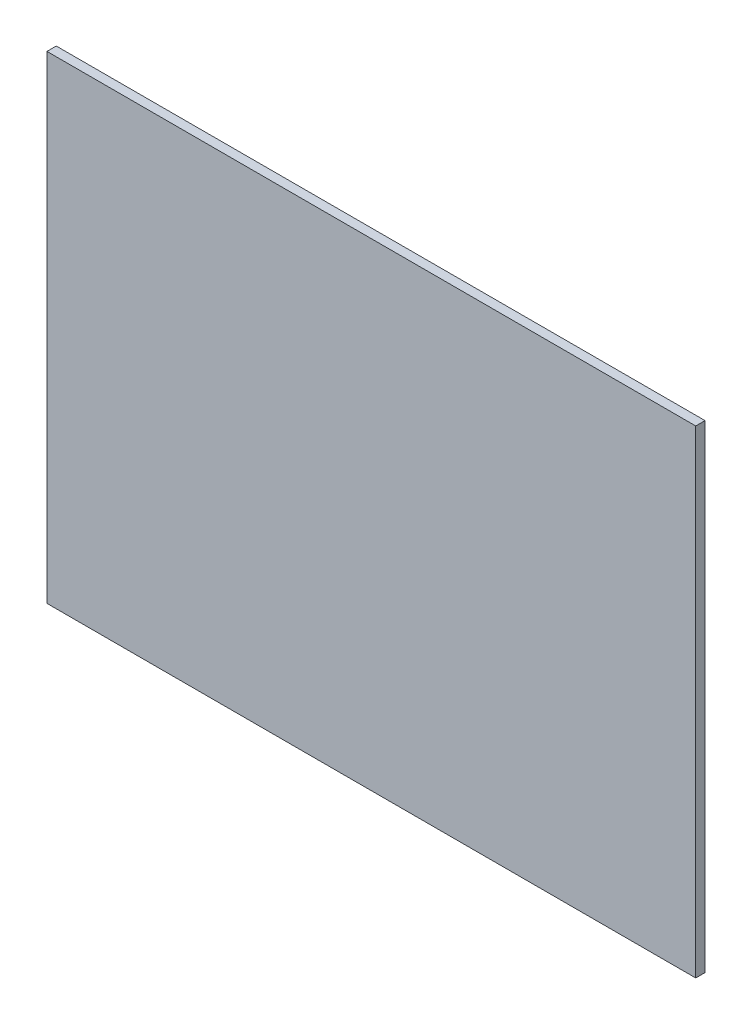
SolidWorks part; units mm, degrees
ref_plane "Front Plane" through (0, 0, 0) normal (0, 0, 1) x (1, 0, 0)
ref_plane "Top Plane" through (0, 0, 0) normal (0, 1, 0) x (1, 0, 0)
ref_plane "Right Plane" through (0, 0, 0) normal (1, 0, 0) x (0, 0, -1)
sketch "Sketch1" plane through (0, 0, 0) normal (0, 0, 1) x (1, 0, 0)
  line L1 (0, 0) -> (418, 0)
  line L2 (0, 0) -> (0, 308)
  line L3 (0, 308) -> (418, 308)
  line L4 (418, 0) -> (418, 308)
  dimension "D1" = 418
  dimension "D2" = 308
extrude "Boss-Extrude1" add sketch "Sketch1" along normal blind 6
